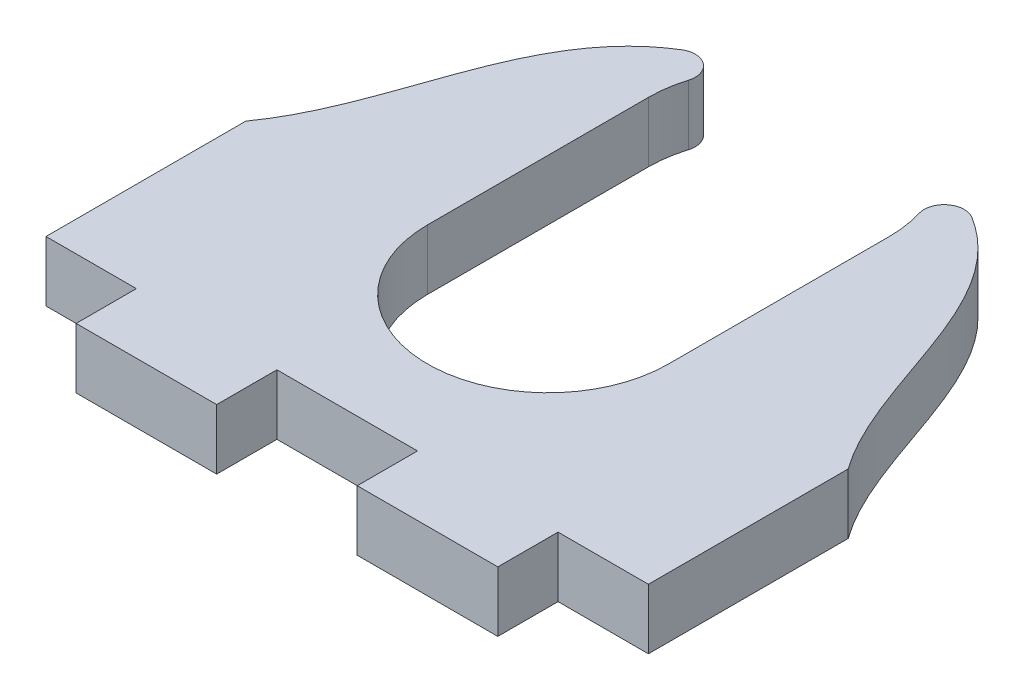
SolidWorks part; units mm, degrees
material "PC High Viscosity"
ref_plane "Front Plane" through (0, 0, 0) normal (0, 0, 1) x (1, 0, 0)
ref_plane "Top Plane" through (0, 0, 0) normal (0, 1, 0) x (1, 0, 0)
ref_plane "Right Plane" through (0, 0, 0) normal (1, 0, 0) x (0, 0, -1)
sketch "Sketch1" plane through (0, 0, 0) normal (0, 1, 0) x (1, 0, 0)
  line L0 (0, -12.5) -> (0, 12.5) construction
  line L1 (-15, -12.5) -> (15, -12.5)
  line L2 (-15, -12.5) -> (-15, 12.5)
  line L3 (-15, 12.5) -> (15, 12.5)
  line L4 (15, -12.5) -> (15, 12.5)
  line L5 (-15, -12.5) -> (15, 12.5) construction
  line L6 (-15, 12.5) -> (15, -12.5) construction
  line L7 (-10.5, -12.5) -> (-3.5, -12.5)
  line L8 (-10.5, -12.5) -> (-10.5, -15.5)
  line L9 (-10.5, -15.5) -> (-3.5, -15.5)
  line L10 (-3.5, -12.5) -> (-3.5, -15.5)
  line L12 (3.5, -12.5) -> (10.5, -12.5)
  line L13 (3.5, -12.5) -> (3.5, -15.5)
  line L14 (3.5, -15.5) -> (10.5, -15.5)
  line L15 (10.5, -12.5) -> (10.5, -15.5)
  point P0 (0, 0)
  dimension "D1" = 30
  dimension "D2" = 25
  dimension "D3" = 7
  dimension "D4" = 7
  dimension "D5" = 3
extrude "Boss-Extrude1" add sketch "Sketch1" along normal blind 3 contours L1 L4 L3 L2 | L10 L1 L8 L9 | L15 L1 L13 L14
sketch "Sketch2" plane through (0, 3, 0) normal (0, 1, 0) x (1, 0, 0)
  line L0 (-4.4721, 12.5) -> (-15, 12.5)
  line L1 (-15, 12.5) -> (15, 12.5) construction
  line L2 (-15, 12.5) -> (-15, -2.55)
  line L3 (-15, -12.5) -> (-15, 12.5) construction
  line L4 (0, 8.5) -> (0, -2.5) construction
  line L5 (6, 8.5) -> (6, -2.5)
  line L6 (-6, 8.5) -> (-6, -2.5)
  line L7 (0, -12.5) -> (0, 12.5) construction
  line L8 (-3.5, -12.5) -> (3.5, -12.5) construction
  line L9 (15, 12.5) -> (15, -2.55)
  line L10 (4.4721, 12.5) -> (15, 12.5)
  arc A0 (6, 8.5) -> (-6, 8.5) centre (0, 8.5) ccw
  arc A1 (-6, -2.5) -> (6, -2.5) centre (0, -2.5) ccw
  spline S0 degree 3 poles (-15, -2.55) (-11.339, 2.5584) (-12.1028, 10.6605) (-4.4721, 12.5) knots 0 0 0 0 1 1 1 1
  spline S1 degree 3 poles (15, -2.55) (11.339, 2.5584) (12.1028, 10.6605) (4.4721, 12.5) knots 0 0 0 0 1 1 1 1
  point P12 (0, 3)
  line M13 (15, -12.5) -> (15, 12.5)
  line M14 (15, 12.5) -> (-15, 12.5)
  line M15 (-15, 12.5) -> (-15, -12.5)
  dimension "D2" = 10
  dimension "D1" = 12
  dimension "D3" = 4
extrude "Cut-Extrude1" cut sketch "Sketch2" against normal through all contours S0 M15 M14 | L6 A1 L5 M14 | S1 M13 M14
fillet "Fillet1" radius 1 2 edges at (-4.4721, 1.5, -12.5) (4.4721, 1.5, -12.5)
equation "\"pulley_pitch_diam\"= 12.73mm"
equation "\"pulley_total_width\"= 16mm"
equation "\"pulley_total_diam\"= 16mm"
equation "\"belt_width\"= 6mm"
equation "\"material_thickness\"= 3mm"
equation "\"shaft_diam\"= 8mm"
equation "\"bearing_od\"= 22mm"
equation "\"bearing_thickness\"= 7mm"
equation "\"D1@Boss-Extrude1\"=\"material_thickness\""
equation "\"D5@Sketch1\"=\"material_thickness\""
